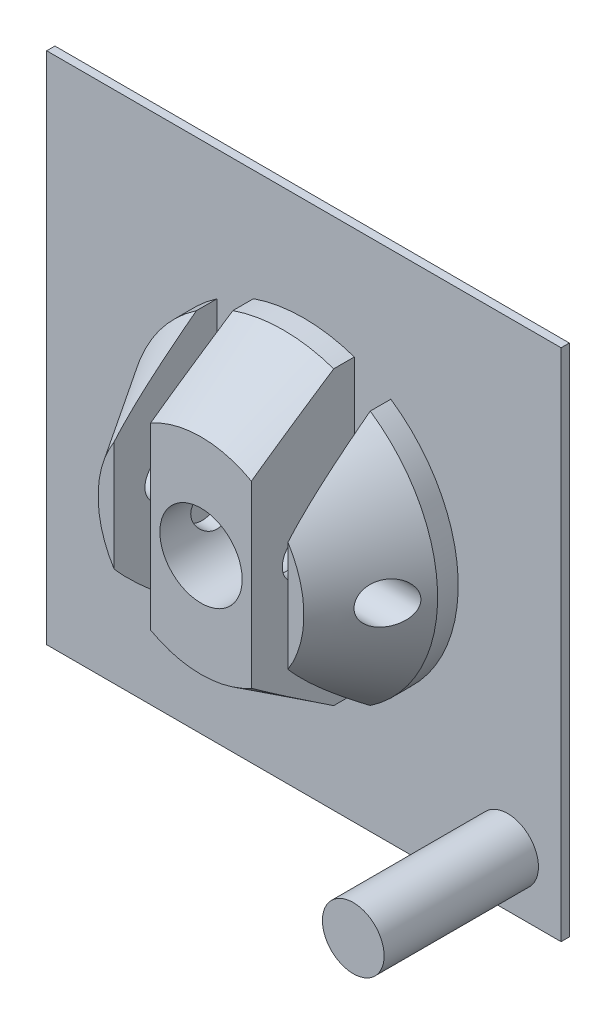
SolidWorks part; units mm, degrees
ref_plane "Alzado" through (0, 0, 0) normal (0, 0, 1) x (1, 0, 0)
ref_plane "Planta" through (0, 0, 0) normal (0, 1, 0) x (1, 0, 0)
ref_plane "Vista lateral" through (0, 0, 0) normal (1, 0, 0) x (0, 0, -1)
sketch "Croquis1" plane through (0, 0, 0) normal (0, 0, 1) x (1, 0, 0)
  line L1 (25, -25) -> (-25, -25)
  line L2 (25, -25) -> (25, 25)
  line L3 (25, 25) -> (-25, 25)
  line L4 (-25, -25) -> (-25, 25)
  line L5 (25, -25) -> (-25, 25) construction
  line L6 (25, 25) -> (-25, -25) construction
  circle A0 centre (0, 0) radius 2
  point P0 (0, 0)
  dimension "D3" = 4
  dimension "D1" = 50
  dimension "D2" = 50
extrude "Saliente-Extruir2" add sketch "Croquis1" along normal blind 0.8
ref_plane "Plano1" through (0, 0, 0) normal (1, 0, 0) x (0, 0, -1)
sketch "Croquis2" plane through (0, 0, 0) normal (1, 0, 0) x (0, 0, -1)
  line L0 (-0.8, 0) -> (-10.8, 0)
  line L1 (-0.8, 25) -> (-0.8, -25) construction
  line L2 (-10.8, 0) -> (-10.8, 10)
  line L3 (-0.8, 15) -> (-2.8, 15)
  line L4 (-0.8, 15) -> (-0.8, 0)
  line L5 (-2.8, 15) -> (-10.8, 10)
  dimension "D1" = 10
  dimension "D2" = 10
  dimension "D3" = 2
  dimension "D4" = 15
revolve "Revolución1" add sketch "Croquis2" angle 360 about L0
sketch "Croquis4" plane through (0, 0, 10.8) normal (0, 0, 1) x (1, 0, 0)
  line L0 (0, -0.44) -> (0, 0.44) construction
  line L1 (-8.45, 20) -> (-4.9, 20)
  line L2 (-8.45, 20) -> (-8.45, -20)
  line L3 (-8.45, -20) -> (-4.9, -20)
  line L4 (-4.9, 20) -> (-4.9, -20)
  line L5 (8.45, -20) -> (4.9, -20)
  line L6 (4.9, 20) -> (4.9, -20)
  line L7 (8.45, 20) -> (4.9, 20)
  line L8 (8.45, 20) -> (8.45, -20)
  circle A0 centre (0, 0) radius 4
  point P6 (-4.9, 0)
  dimension "D4" = 8
  dimension "D1" = 3.55
  dimension "D2" = 4.9
  dimension "D3" = 40
extrude "Cortar-Extruir1" cut sketch "Croquis4" against normal up to vertex (10 mm away) up to point (-25, 25, 0.8)
sketch "Croquis7" plane through (-25, 0, 0) normal (-1, 0, 0) x (0, 0, 1)
  line L0 (0.8, -12.3934) -> (0.8, 12.3934) construction
  circle A0 centre (5.8, 0) radius 2
  dimension "D1" = 4
  dimension "D2" = 5
extrude "Cortar-Extruir2" cut sketch "Croquis7" against normal up to vertex
sketch "Croquis8" plane through (0, 0, 0.8) normal (0, 0, 1) x (1, 0, 0)
  line L1 (22.8, -19.8) -> (25, -19.8) construction
  line L2 (25, -25) -> (25, 25) construction
  line L3 (19.8, -22.8) -> (19.8, -25) construction
  line L4 (-25, -25) -> (25, -25) construction
  circle A0 centre (19.8, -19.8) radius 3
  dimension "D1" = 2.2
  dimension "D3" = 6
  dimension "D2" = 2.2
extrude "Saliente-Extruir3" add sketch "Croquis8" along normal blind 15
